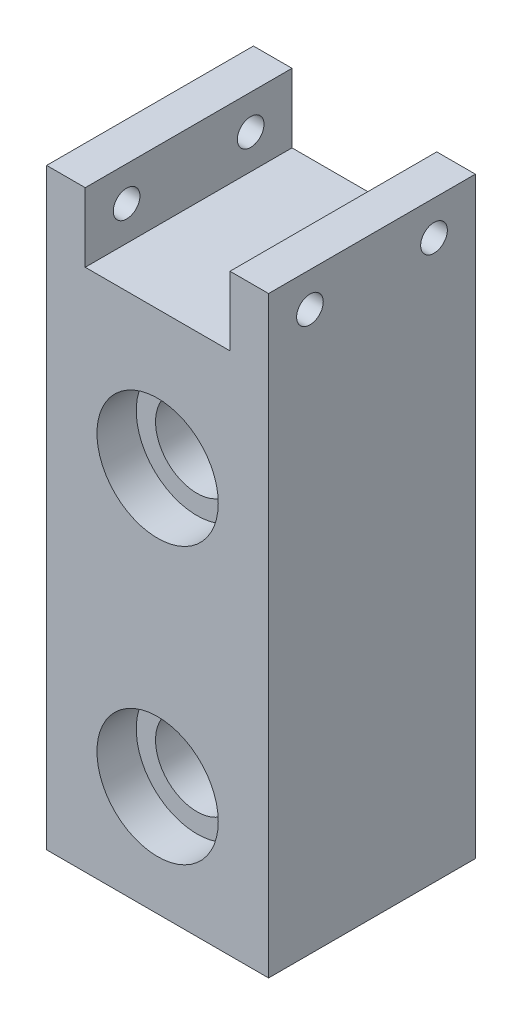
SolidWorks part; units mm, degrees
ref_plane "Front Plane" through (0, 0, 0) normal (0, 0, 1) x (1, 0, 0)
ref_plane "Top Plane" through (0, 0, 0) normal (0, 1, 0) x (1, 0, 0)
ref_plane "Right Plane" through (0, 0, 0) normal (1, 0, 0) x (0, 0, -1)
sketch "Sketch1" plane through (0, 0, 0) normal (0, 0, 1) x (1, 0, 0)
  line L0 (13.335, 25.4) -> (-13.335, 25.4)
  line L1 (-13.335, 25.4) -> (-13.335, 38.1)
  line L2 (-13.335, 38.1) -> (-20.447, 38.1)
  line L3 (-20.447, 38.1) -> (-20.447, -71.12)
  line L4 (-20.447, -71.12) -> (20.447, -71.12)
  line L5 (0, 0) -> (0, 45.5255) construction
  line L6 (20.447, 38.1) -> (20.447, -71.12)
  line L7 (13.335, 38.1) -> (20.447, 38.1)
  line L8 (13.335, 25.4) -> (13.335, 38.1)
  point P7 (0, -71.12)
  point P15 (0, 25.4)
  dimension "D1" = 25.4
  dimension "D2" = 12.7
  dimension "D3" = 7.112
  dimension "D4" = 71.12
  dimension "D5" = 13.335
extrude "Boss-Extrude1" add sketch "Sketch1" along normal mid plane 38.1
sketch "Sketch7" plane through (0, 0, 19.05) normal (0, 0, 1) x (1, 0, 0)
  circle A0 centre (0, 0) radius 7.62
  circle A1 centre (0, -50.8) radius 7.62
  point P5 (0, 0)
  dimension "D1" = 15.24
  dimension "D2" = 15.24
  dimension "D3" = 50.8
extrude "Cut-Extrude2" cut sketch "Sketch7" against normal up to surface (38.1 mm away) up to face at (0, 7.62, -19.05)
sketch "Sketch2" plane through (0, 0, 19.05) normal (0, 0, 1) x (1, 0, 0)
  circle A0 centre (0, 0) radius 11.176
  circle A1 centre (0, -50.8) radius 11.176
  dimension "D1" = 22.352
  dimension "D3" = 22.352
  dimension "D2" = 50.8
extrude "Cut-Extrude1" cut sketch "Sketch2" along direction (0, 0, -1) on the side against the normal blind 7.239
sketch "Sketch8" plane through (0, 0, -19.05) normal (0, 0, 1) x (1, 0, 0)
  circle A0 centre (0, 0) radius 11.176
  circle A1 centre (0, -50.8) radius 11.176
  dimension "D1" = 22.352
  dimension "D3" = 22.352
  dimension "D2" = 50.8
extrude "Cut-Extrude3" cut sketch "Sketch8" along normal blind 7.239
hole_wizard "#10 (0.1935) Diameter Hole1" positions "Sketch5" profile "Sketch6" hole size "#10" standard "ANSI Inch" end condition through all
sketch "Sketch5" plane through (20.447, 0, 0) normal (1, 0, 0) x (0, 0, -1)
  point P0 (-11.43, 31.75)
  dimension "D1" = 11.43
  dimension "D2" = 31.75
sketch "Sketch6" plane through (20.447, 31.75, 11.43) normal (0, 1, 0) x (0, 0, -1)
  line L0 (0, 0) -> (0, 40.894)
  line L1 (0, 40.894) -> (2.4574, 40.894)
  line L2 (2.4574, 40.894) -> (2.4574, 0)
  line L5 (2.4574, 0) -> (0, 0)
  line L11 (0, -6.35) -> (0, 107.95) construction
  dimension "Thru Hole Dia." = 4.9149
  dimension "Thru Hole Depth" = 40.894
mirror "Mirror1" about plane through (0, 0, 0) normal (0, 0, 1) of "#10 (0.1935) Diameter Hole1"
